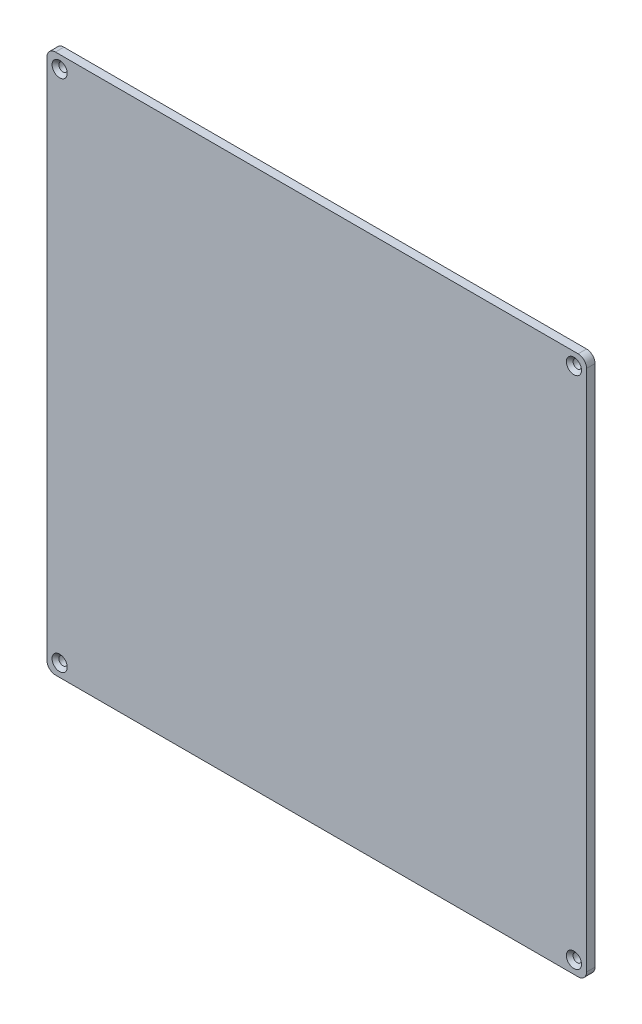
SolidWorks part; units mm, degrees
ref_plane "Plan de face" through (0, 0, 0) normal (0, 0, 1) x (1, 0, 0)
ref_plane "Plan de dessus" through (0, 0, 0) normal (0, 1, 0) x (1, 0, 0)
ref_plane "Plan de droite" through (0, 0, 0) normal (1, 0, 0) x (0, 0, -1)
sketch "Esquisse1" plane through (0, 0, 0) normal (0, 0, 1) x (1, 0, 0)
  line L0 (160, 320) -> (160, 0) construction
  line L1 (0, 0) -> (320, 0)
  line L2 (0, 0) -> (0, 320)
  line L3 (0, 320) -> (320, 320)
  line L4 (320, 0) -> (320, 320)
  line L5 (160, 0) -> (320, 160) construction
  line L6 (320, 160) -> (0, 160) construction
  circle A0 centre (7.5, 312.5) radius 2.5
  circle A1 centre (312.5, 312.5) radius 2.5
  circle A2 centre (7.5, 7.5) radius 2.5
  circle A3 centre (312.5, 7.5) radius 2.5
  dimension "D2" = 7.5
  dimension "D4" = 5
  dimension "D1" = 320
  dimension "D3" = 7.5
extrude "Boss.-Extru.1" add sketch "Esquisse1" along normal blind 5
fillet "Congé1" radius 5 4 edges at (0, 0, 2.5) (320, 0, 2.5) (320, 320, 2.5) (0, 320, 2.5)
chamfer "Chanfrein1" distance 2 angle 45 4 edges at (315, 312.5, 5) (10, 312.5, 5) (10, 7.5, 5) (315, 7.5, 5)
